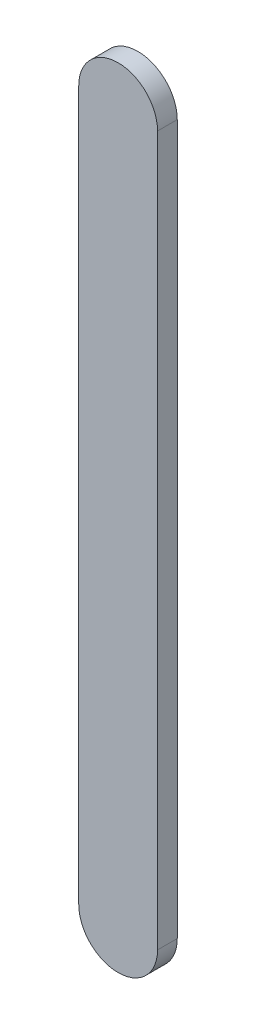
SolidWorks part; units mm, degrees
ref_plane "前视基准面" through (0, 0, 0) normal (0, 0, 1) x (1, 0, 0)
ref_plane "上视基准面" through (0, 0, 0) normal (0, 1, 0) x (1, 0, 0)
ref_plane "右视基准面" through (0, 0, 0) normal (1, 0, 0) x (0, 0, -1)
sketch "草图1" plane through (0, 0, 0) normal (0, 0, 1) x (1, 0, 0)
  line L0 (0, 0) -> (0, -180) construction
  line L1 (10, 0) -> (10, -180)
  line L2 (-10, 0) -> (-10, -180)
  arc A0 (10, 0) -> (-10, 0) centre (0, 0) ccw
  arc A1 (-10, -180) -> (10, -180) centre (0, -180) ccw
  point P3 (0, -90)
extrude "凸台-拉伸1" add sketch "草图1" along normal blind 5
